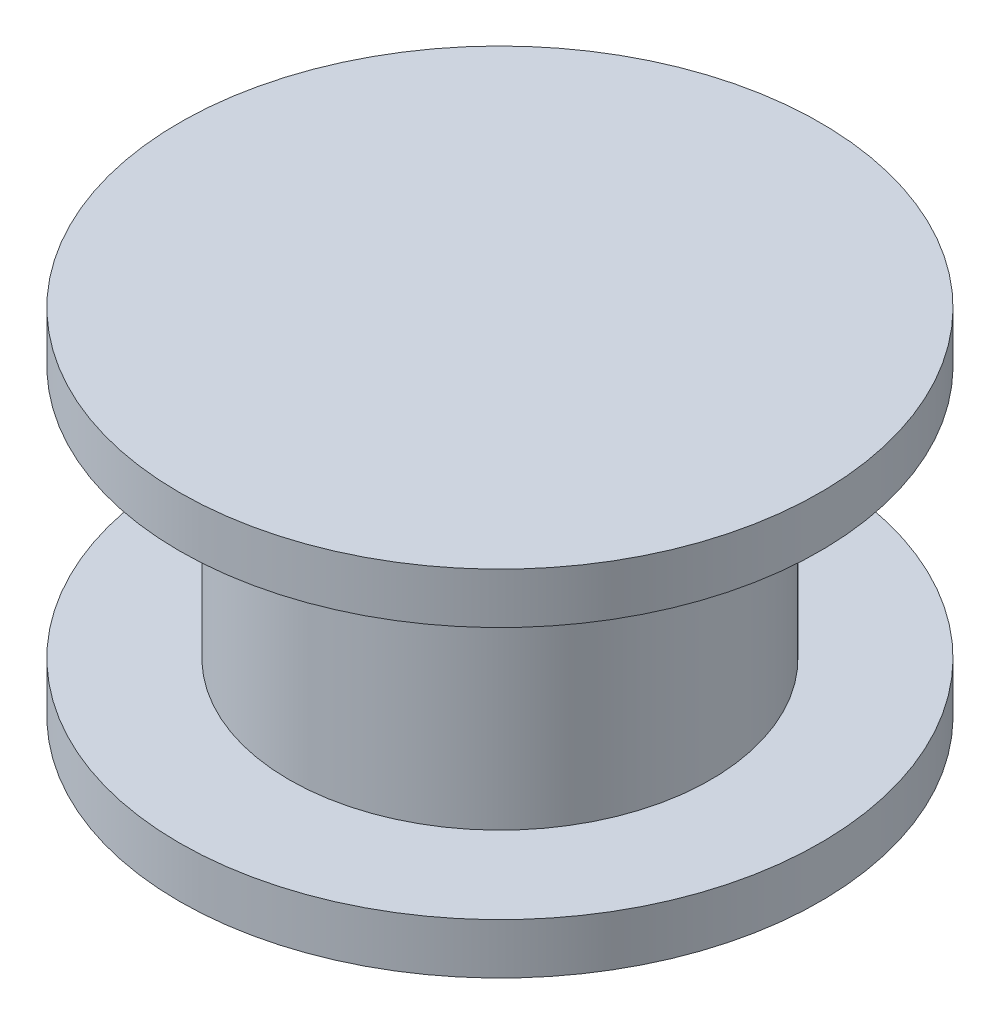
SolidWorks part; units mm, degrees
ref_plane "Front Plane" through (0, 0, 0) normal (0, 0, 1) x (1, 0, 0)
ref_plane "Top Plane" through (0, 0, 0) normal (0, 1, 0) x (1, 0, 0)
ref_plane "Right Plane" through (0, 0, 0) normal (1, 0, 0) x (0, 0, -1)
sketch "Sketch1" plane through (0, 0, 0) normal (0, 1, 0) x (1, 0, 0)
  circle A0 centre (0, 0) radius 9.5
  dimension "D1" = 19
extrude "Boss-Extrude1" add sketch "Sketch1" along normal blind 1.5
sketch "Sketch2" plane through (0, 1.5, 0) normal (0, 1, 0) x (1, 0, 0)
  circle A0 centre (0, 0) radius 6.25
  dimension "D1" = 12.5
extrude "Boss-Extrude2" add sketch "Sketch2" along normal blind 7.5
sketch "Sketch4" plane through (0, 9, 0) normal (0, 1, 0) x (1, 0, 0)
  circle A0 centre (0, 0) radius 9.5
  dimension "D1" = 19
extrude "Boss-Extrude4" add sketch "Sketch4" along normal blind 1.5 contours A0
